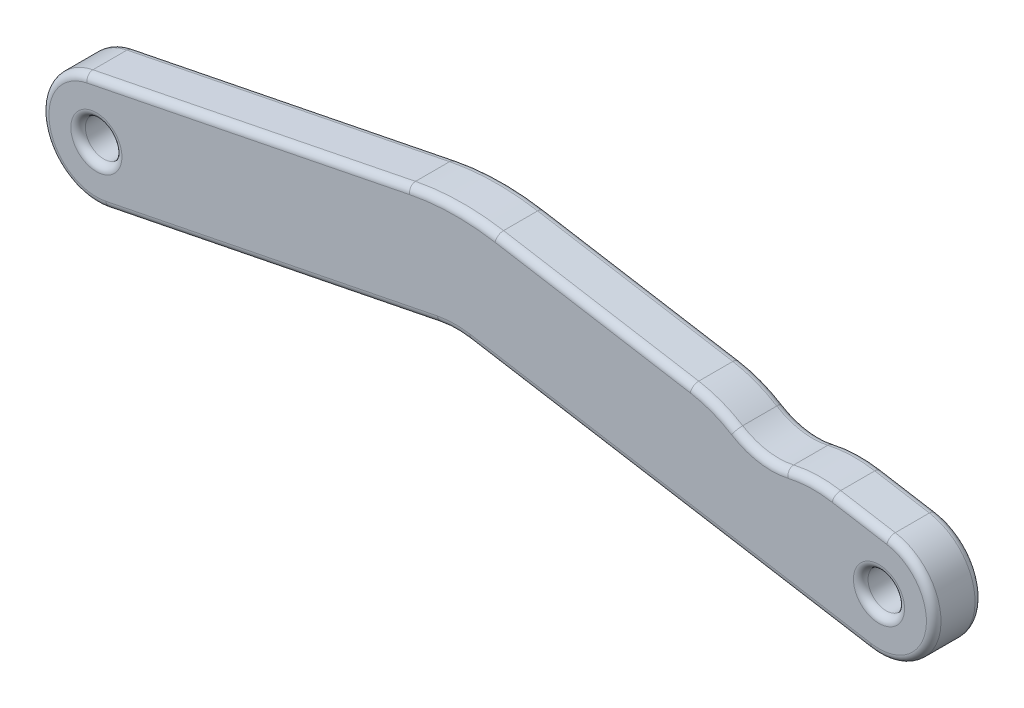
SolidWorks part; units mm, degrees
ref_plane "Front" through (0, 0, 0) normal (0, 0, 1) x (1, 0, 0)
ref_plane "Top" through (0, 0, 0) normal (0, 1, 0) x (1, 0, 0)
ref_plane "Right" through (0, 0, 0) normal (1, 0, 0) x (0, 0, -1)
sketch "Sketch1" plane through (0, 0, 0) normal (0, 0, 1) x (1, 0, 0)
  line L0 (0, 0) -> (32.1759, 0) construction
  line L1 (0, 2.25) -> (32.1759, 2.25)
  line L2 (0, -2.25) -> (32.1759, -2.25)
  circle A0 centre (0, 0) radius 0.75
  arc A1 (0, 2.25) -> (0, -2.25) centre (0, 0) ccw
  arc A2 (32.1759, -2.25) -> (32.1759, 2.25) centre (32.1759, 0) ccw
  circle A3 centre (32.1759, 0) radius 0.75
  point P3 (16.0879, 0)
  dimension "D1" = 1.5
  dimension "D2" = 32.1759
  dimension "D3" = 1.5
extrude "Boss-Extrude1" add sketch "Sketch1" along normal blind 2
sketch "Sketch2" plane through (0, 0, 0) normal (0, 0, 1) x (1, 0, 0)
  line L0 (12.0571, -0.5571) -> (14.4503, 0.4122)
  line L1 (15.3955, 0.2207) -> (16.4724, -0.5571)
  line L2 (16.4724, -0.5571) -> (17.3174, -2.6432)
  line L3 (17.3174, -2.6432) -> (12.0571, -3.2881)
  line L4 (12.0571, -3.2881) -> (12.0571, -0.5571)
  arc A0 (14.4503, 0.4122) -> (15.3955, 0.2207) centre (14.7783, -0.3977) cw
sketch "Sketch3" plane through (0, 0, 0) normal (0, 0, 1) x (1, 0, 0)
  line L0 (0.4422, -2.2061) -> (14.0789, 0.5271)
  line L1 (15.3224, 0.5467) -> (31.8035, -2.219)
  line L2 (-0.4422, 2.2061) -> (12.8219, 4.8647)
  line L3 (16.4421, 4.9218) -> (32.5482, 2.219)
  circle A0 centre (0, 0) radius 2.25 construction
  arc A1 (14.0789, 0.5271) -> (15.3224, 0.5467) centre (14.754, -2.8408) cw
  arc A2 (31.8035, -2.219) -> (32.5482, 2.219) centre (32.1759, 0) ccw
  arc A3 (32.1759, -2.25) -> (32.1759, 2.25) centre (32.1759, 0) ccw construction
  circle A4 centre (32.1759, 0) radius 0.75 construction
  arc A5 (0.4422, -2.2061) -> (-0.4422, 2.2061) centre (0, 0) cw
  arc A6 (0, 2.25) -> (0, -2.25) centre (0, 0) ccw construction
  arc A7 (12.8219, 4.8647) -> (16.4421, 4.9218) centre (14.7871, -4.9403) cw
  point P17 (28.4872, 2.2061)
  point P24 (27.4873, -2.2061)
  dimension "D1" = 10
extrude "Cut-Extrude4" cut sketch "Sketch3" along normal through all flip side to cut
sketch "Sketch4" plane through (0, 0, 2) normal (0, 0, 1) x (1, 0, 0)
  line L4 (12.8219, 4.8647) -> (-0.4422, 2.2061)
  line L5 (32.5482, 2.219) -> (16.4421, 4.9218)
  line L6 (15.3224, 0.5467) -> (31.8035, -2.219)
  line L7 (0.4422, -2.2061) -> (14.0789, 0.5271)
  line L8 (12.8219, 4.8647) -> (-0.4422, 2.2061)
  line L9 (32.5482, 2.219) -> (16.4421, 4.9218)
  line L10 (15.3224, 0.5467) -> (31.8035, -2.219)
  line L11 (0.4422, -2.2061) -> (14.0789, 0.5271)
  circle A0 centre (32.1759, 0) radius 0.75 construction
  circle A1 centre (0, 0) radius 0.75 construction
  circle A2 centre (32.1759, 0) radius 0.75
  circle A3 centre (0, 0) radius 0.75
  arc A4 (16.4421, 4.9218) -> (12.8219, 4.8647) centre (14.7871, -4.9403) ccw
  arc A5 (31.8035, -2.219) -> (32.5482, 2.219) centre (32.1759, 0) ccw
  arc A6 (15.3224, 0.5467) -> (14.0789, 0.5271) centre (14.754, -2.8408) ccw
  arc A7 (-0.4422, 2.2061) -> (0.4422, -2.2061) centre (0, 0) ccw
  arc A8 (16.4421, 4.9218) -> (12.8219, 4.8647) centre (14.7871, -4.9403) ccw
  arc A9 (31.8035, -2.219) -> (32.5482, 2.219) centre (32.1759, 0) ccw
  arc A10 (15.3224, 0.5467) -> (14.0789, 0.5271) centre (14.754, -2.8408) ccw
  arc A11 (-0.4422, 2.2061) -> (0.4422, -2.2061) centre (0, 0) ccw
  dimension "D1" = 0
extrude "Boss-Extrude2" add sketch "Sketch4" against normal up to vertex
sketch3d "3DSketch2"
  line L8 (28.5539, 2.4862, 2) -> (20.7366, 4.2679, 2)
  line L9 (30.5553, 5.4776, 2) -> (31.9718, 1.7671, 2)
  line L10 (18.1052, 9.4862, 2) -> (17.7608, 10.5197, 2)
  line L11 (20.8202, 8.9829, 2) -> (18.1052, 9.4862, 2)
  arc A18 (30.4787, 0.5435, 2) -> (28.5539, 2.4862, 2) centre (27.9872, 0, 2) ccw
  arc A19 (29.7103, 7.668, 2) -> (30.5553, 5.4776, 2) centre (-281.7577, -113.7456, 2) ccw
  arc A20 (25.106, 12.1538, 2) -> (29.7103, 7.668, 2) centre (22.4753, 4.8477, 2) ccw
  arc A21 (21.1241, 8.8735, 2) -> (20.8202, 8.9829, 2) centre (20.6379, 7.9997, 2) ccw
  arc A22 (26.5449, 8.4396, 2) -> (21.1241, 8.8735, 2) centre (23.5636, 5.2719, 2) ccw
  arc A23 (25.3798, 7.2017, 2) -> (26.5449, 8.4396, 2) centre (25.9623, 7.8207, 2) ccw
  arc A24 (21.6394, 7.094, 2) -> (25.3798, 7.2017, 2) centre (23.5636, 5.2719, 2) ccw
  arc A25 (20.9991, 6.8287, 2) -> (21.6394, 7.094, 2) centre (21.0222, 7.6784, 2) ccw
  arc A26 (20.7366, 4.2679, 2) -> (20.9991, 6.8287, 2) centre (23.5636, 5.2719, 2) ccw
  spline S12 degree 3 poles (31.0836, 0.7536, 2) (30.8819, 0.6835, 2) (30.6803, 0.6135, 2) (30.4787, 0.5435, 2) knots 0 0 0 0 1 1 1 1
  spline S13 degree 3 poles (31.9718, 1.7671, 2) (31.9394, 1.656, 2) (31.8982, 1.5432, 2) (31.793, 1.3329, 2) (31.7287, 1.2339, 2) (31.5778, 1.0565, 2) (31.4894, 0.9764, 2) (31.2983, 0.8449, 2) (31.195, 0.7923, 2) (31.0836, 0.7536, 2) knots 0 0 0 0 0.25 0.25 0.5 0.5 0.75 0.75 1 1 1 1
  spline S14 degree 3 poles (21.9785, 12.5206, 2) (22.5054, 12.5209, 2) (23.0298, 12.4877, 2) (24.0747, 12.3695, 2) (24.5956, 12.2784, 2) (25.106, 12.1538, 2) knots 0 0 0 0 0.5 0.5 1 1 1 1
  spline S15 degree 3 poles (21.2302, 12.2749, 2) (21.4793, 12.3579, 2) (21.7264, 12.4476, 2) (21.9785, 12.5206, 2) knots 0 0 0 0 1 1 1 1
  spline S16 degree 3 poles (19.5527, 11.5132, 2) (19.7933, 11.7049, 2) (20.0675, 11.854, 2) (20.6399, 12.0887, 2) (20.9367, 12.1771, 2) (21.2302, 12.2749, 2) knots 0 0 0 0 0.5 0.5 1 1 1 1
  spline S17 degree 3 poles (17.7608, 10.5197, 2) (18.4099, 10.7525, 2) (19.009, 11.0801, 2) (19.5527, 11.5132, 2) knots 0 0 0 0 1 1 1 1
  point P53 (27.9872, 0, 4.55)
  point P54 (-281.7577, -113.7456, -332.2957)
  point P55 (22.4753, 4.8477, -5.7653)
  point P56 (20.6379, 7.9997, 3)
  point P57 (23.5636, 5.2719, 6.35)
  point P58 (25.9623, 7.8207, 2.85)
  point P59 (23.5636, 5.2719, -0.65)
  point P60 (21.0222, 7.6784, 2.85)
  point P61 (23.5636, 5.2719, -1)
sketch3d "3DSketch4"
  line L10 (32.7394, 2.487, -2.25) -> (29.3355, 3.0582, -2.25)
  line L11 (32.9472, -5.4542, -2.25) -> (34.5792, -0.8523, -2.25)
  line L12 (22.5413, -4.8957, -2.25) -> (32.9472, -5.4542, -2.25)
  line L13 (18.3133, 5.1916, -2.25) -> (22.5413, -4.8957, -2.25)
  line L14 (25.0231, 6.5178, -2.25) -> (18.3133, 5.1916, -2.25)
  arc A8 (34.5792, -0.8523, -2.25) -> (32.7394, 2.487, -2.25) centre (32.1759, 0, -2.25) ccw
  arc A9 (25.8566, 3.642, -2.25) -> (25.0231, 6.5178, -2.25) centre (28.591, 5.9931, -2.25) ccw
  arc A10 (28.7649, 2.9862, -2.25) -> (25.8566, 3.642, -2.25) centre (27.7522, 5.2719, -2.25) ccw
  arc A11 (29.3355, 3.0582, -2.25) -> (28.7649, 2.9862, -2.25) centre (29.17, 2.072, -2.25) ccw
  point P25 (32.1759, 0, 0.3)
  point P26 (28.591, 5.9931, -5.8562)
  point P27 (27.7522, 5.2719, -4.75)
  point P28 (29.17, 2.072, -1.25)
sketch "Sketch6" plane through (0, 0, 0) normal (0, 0, 1) x (1, 0, 0)
  line L7 (32.5482, 2.219) -> (16.4421, 4.9218) construction
  line L8 (24.4675, 3.575) -> (23.959, 3.6603)
  line L9 (23.959, 3.6603) -> (27.3633, 6.2663)
  line L10 (27.3633, 6.2663) -> (30.3031, 2.5957)
  arc A5 (26.276, 2.8927) -> (28.3708, 2.5411) centre (27.7522, 5.2719) ccw
  arc A6 (25.8566, 3.642) -> (28.7649, 2.9862) centre (27.7522, 5.2719) ccw construction
  arc A7 (30.3031, 2.5957) -> (28.3708, 2.5411) centre (29.4756, -2.3353) ccw
  arc A8 (24.4675, 3.575) -> (26.276, 2.8927) centre (23.64, -1.356) cw
  dimension "D1" = 0.3
  dimension "D2" = 5
extrude "Cut-Extrude6" cut sketch "Sketch6" against normal through all and the other way through all
fillet "Fillet1" radius 0.3 28 edges at (32.9259, 0, 0) (0.75, 0, 0) (7.2606, -0.8395, 0) (14.6998, 0.5937, 0) (23.563, -0.8361, 0) (14.6294, 5.0584, 2) (14.6294, 5.0584, 0) (6.1898, 3.5354, 2) (6.1898, 3.5354, 0) (-2.2061, -0.4422, 0) (32.9259, 0, 2) (0.75, 0, 2) (23.563, -0.8361, 2) (14.6998, 0.5937, 2) (7.2606, -0.8395, 2) (-2.2061, -0.4422, 2) (20.4548, 4.2484, 2) (34.3948, -0.3724, 0) (31.4256, 2.4074, 2) (34.3948, -0.3724, 2) (27.2888, 2.5105, 0) (25.405, 3.3221, 2) (27.2888, 2.5105, 2) (29.3343, 2.6627, 2)
